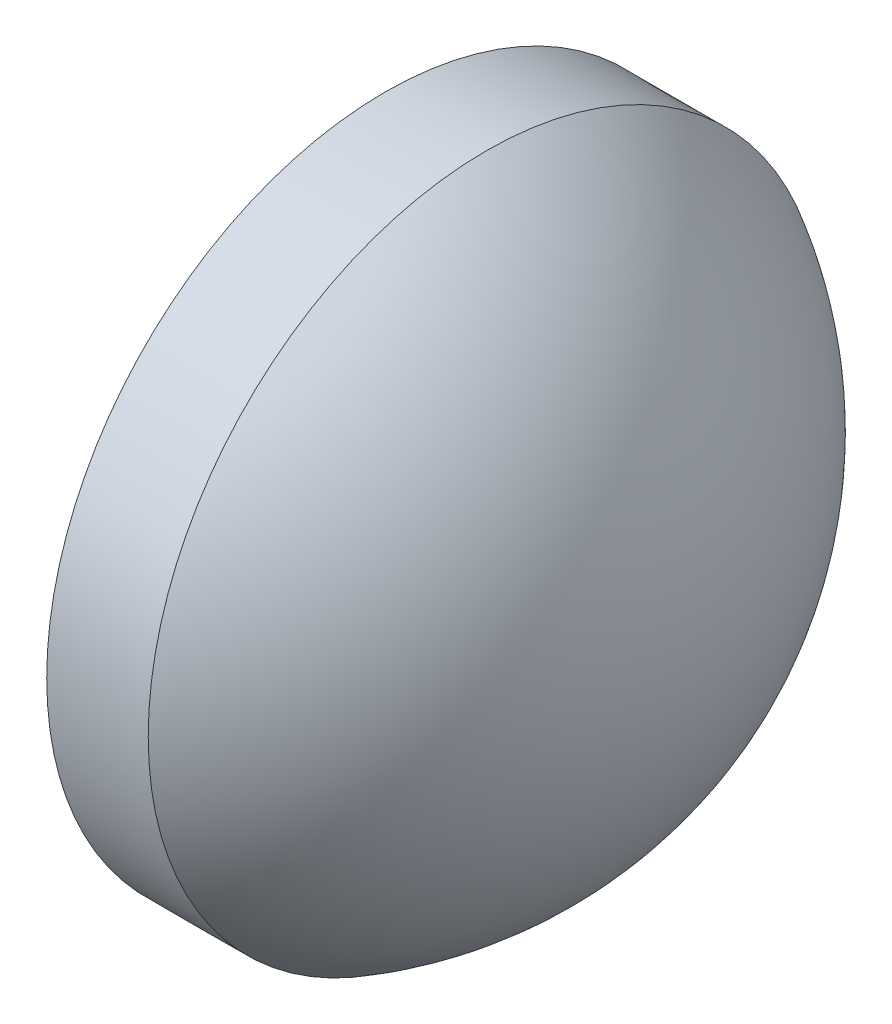
SolidWorks part; units mm, degrees
ref_plane "前视基准面" through (0, 0, 0) normal (0, 0, 1) x (1, 0, 0)
ref_plane "上视基准面" through (0, 0, 0) normal (0, 1, 0) x (1, 0, 0)
ref_plane "右视基准面" through (0, 0, 0) normal (1, 0, 0) x (0, 0, -1)
sketch "草图2" plane through (0, 0, 0) normal (0, 0, 1) x (1, 0, 0)
  line L0 (22.2544, 13.0648) -> (27.775, 13.0654) construction
  line L1 (22.7674, 18.0649) -> (24.2674, 18.0649)
  line L2 (27.1974, 13.0654) -> (22.7674, 13.0649)
  line L5 (22.7674, 13.0649) -> (22.7674, 18.0649)
  arc A0 (27.1974, 13.0654) -> (24.2674, 18.0649) centre (21.4662, 13.0649) ccw
revolve "旋转1" add sketch "草图2" angle 360 about L0
